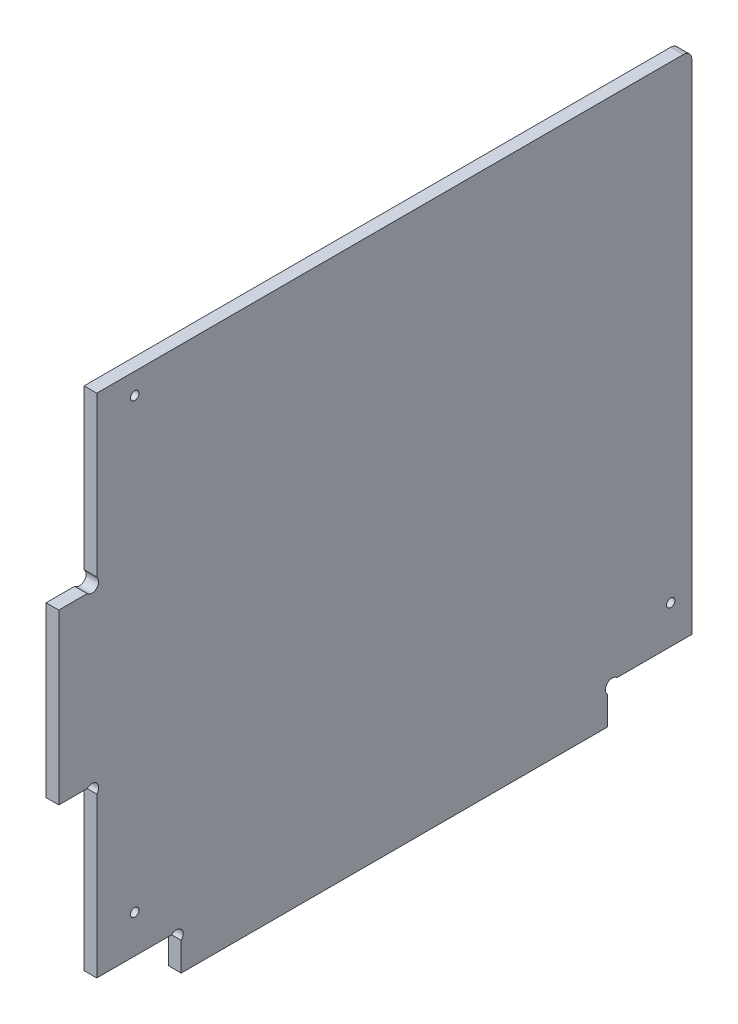
SolidWorks part; units mm, degrees
ref_plane "Plan de face" through (0, 0, 0) normal (0, 0, 1) x (1, 0, 0)
ref_plane "Plan de dessus" through (0, 0, 0) normal (0, 1, 0) x (1, 0, 0)
ref_plane "Plan de droite" through (0, 0, 0) normal (1, 0, 0) x (0, 0, -1)
sketch "Esquisse1" plane through (0, 0, 0) normal (1, 0, 0) x (0, 0, -1)
  line L11 (130, 6.7373) -> (130, 0)
  line L13 (29, 6.7373) -> (29, 0)
  line L14 (0, 49) -> (6.7373, 49)
  line L15 (0, 89) -> (6.7373, 89)
  line L16 (29, 0) -> (130, 0)
  line L17 (26.7373, 9) -> (9, 9)
  line L18 (9, 9) -> (9, 46.7373)
  line L19 (0, 49) -> (0, 89)
  line L20 (9, 91.2627) -> (9, 129)
  line L21 (9, 129) -> (150, 129)
  line L22 (150, 129) -> (150, 9)
  line L23 (150, 9) -> (132.2627, 9)
  arc A0 (132.2627, 9) -> (130, 6.7373) centre (131.1314, 7.8686) ccw
  arc A1 (9, 46.7373) -> (6.7373, 49) centre (7.8686, 47.8686) ccw
  arc A2 (26.7373, 9) -> (29, 6.7373) centre (27.8686, 7.8686) cw
  arc A3 (9, 91.2627) -> (6.7373, 89) centre (7.8686, 90.1314) cw
  dimension "D11" = 20
  dimension "D8" = 1.6
  dimension "D1" = 141
  dimension "D2" = 120
  dimension "D3" = 20
  dimension "D4" = 9
  dimension "D5" = 9
  dimension "D6" = 40
  dimension "D7" = 40
  dimension "D9" = 1.1314
  dimension "D10" = 2.2627
  dimension "D12" = 1.1314
  dimension "D13" = 2.2627
  dimension "D14" = 101
extrude "Extrusion1" add sketch "Esquisse1" along normal blind 3
sketch "Esquisse2" plane through (3, 0, 0) normal (1, 0, 0) x (0, 0, -1)
  line L0 (132.2627, 9) -> (150, 9) construction
  line L1 (150, 9) -> (150, 129) construction
  line L2 (9, 46.7373) -> (9, 9) construction
  line L3 (9, 9) -> (26.7373, 9) construction
  line L5 (150, 129) -> (9, 129) construction
  circle A1 centre (18, 124) radius 1
  circle A2 centre (18, 18) radius 1
  circle A3 centre (145, 18) radius 1
  dimension "D1" = 2
  dimension "D2" = 5
  dimension "D3" = 9
  dimension "D4" = 5
  dimension "D5" = 9
  dimension "D6" = 9
extrude "Enlèv. mat.-Extru.1" cut sketch "Esquisse2" against normal through all
fillet "Congé1" radius 2 1 edges at (1.5, 129, -150)
